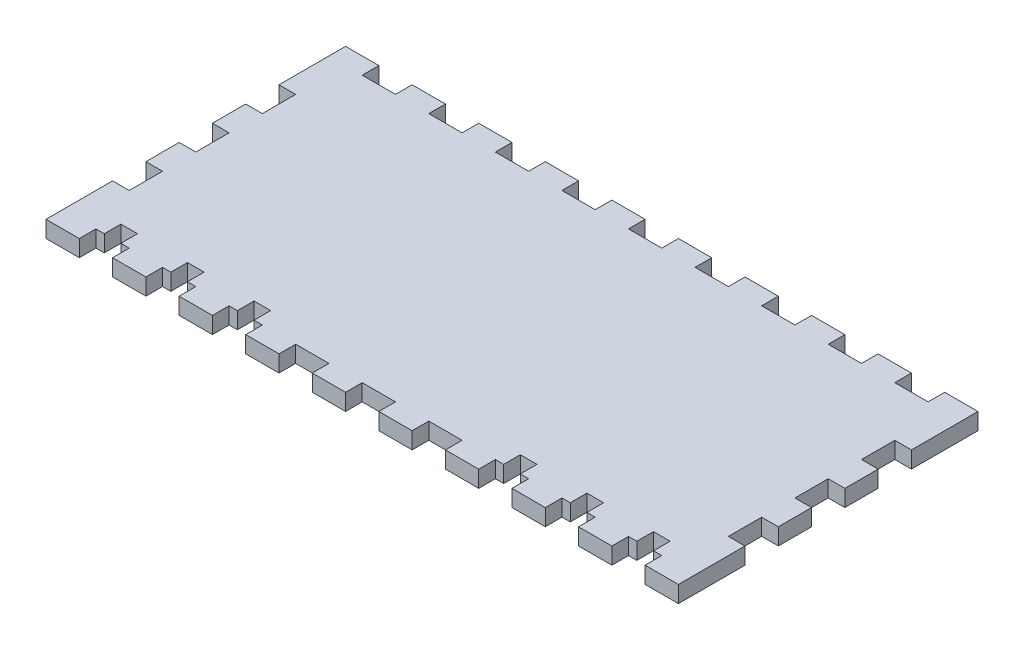
SolidWorks part; units mm, degrees
material "Pine"
ref_plane "Front Plane" through (0, 0, 0) normal (0, 0, 1) x (1, 0, 0)
ref_plane "Top Plane" through (0, 0, 0) normal (0, 1, 0) x (1, 0, 0)
ref_plane "Right Plane" through (0, 0, 0) normal (1, 0, 0) x (0, 0, -1)
sketch "Sketch1" plane through (0, 0, 0) normal (0, 1, 0) x (1, 0, 0)
  line L1 (0, 0) -> (241.3, 0)
  line L2 (0, 0) -> (0, 114.3)
  line L3 (0, 114.3) -> (241.3, 114.3)
  line L4 (241.3, 0) -> (241.3, 114.3)
  dimension "D1" = 114.3
  dimension "D2" = 241.3
extrude "Boss-Extrude1" add sketch "Sketch1" along normal blind 6.35
sketch "Sketch2" plane through (0, 6.35, 0) normal (0, 1, 0) x (1, 0, 0)
  line L0 (25.4, 114.3) -> (12.7, 114.3)
  line L1 (0, 114.3) -> (-12.7, 114.3)
  line L2 (0, 114.3) -> (0, 107.95)
  line L3 (0, 107.95) -> (-12.7, 107.95)
  line L4 (-12.7, 114.3) -> (-12.7, 107.95)
  line L5 (0, 0) -> (-12.7, 0)
  line L6 (0, 0) -> (0, 6.35)
  line L7 (0, 6.35) -> (-12.7, 6.35)
  line L8 (-12.7, 0) -> (-12.7, 6.35)
  line L9 (25.4, 114.3) -> (25.4, 107.95)
  line L10 (25.4, 107.95) -> (12.7, 107.95)
  line L11 (12.7, 114.3) -> (12.7, 107.95)
  line L12 (25.4, 0) -> (12.7, 0)
  line L13 (25.4, 0) -> (25.4, 6.35)
  line L14 (25.4, 6.35) -> (12.7, 6.35)
  line L15 (12.7, 0) -> (12.7, 6.35)
  line L16 (50.8, 114.3) -> (38.1, 114.3)
  line L17 (50.8, 114.3) -> (50.8, 107.95)
  line L18 (50.8, 107.95) -> (38.1, 107.95)
  line L19 (38.1, 114.3) -> (38.1, 107.95)
  line L20 (50.8, 0) -> (38.1, 0)
  line L21 (50.8, 0) -> (50.8, 6.35)
  line L22 (50.8, 6.35) -> (38.1, 6.35)
  line L23 (38.1, 0) -> (38.1, 6.35)
  line L24 (76.2, 114.3) -> (63.5, 114.3)
  line L25 (76.2, 114.3) -> (76.2, 107.95)
  line L26 (76.2, 107.95) -> (63.5, 107.95)
  line L27 (63.5, 114.3) -> (63.5, 107.95)
  line L28 (76.2, 0) -> (63.5, 0)
  line L29 (76.2, 0) -> (76.2, 6.35)
  line L30 (76.2, 6.35) -> (63.5, 6.35)
  line L31 (63.5, 0) -> (63.5, 6.35)
  line L32 (101.6, 114.3) -> (88.9, 114.3)
  line L33 (101.6, 114.3) -> (101.6, 107.95)
  line L34 (101.6, 107.95) -> (88.9, 107.95)
  line L35 (88.9, 114.3) -> (88.9, 107.95)
  line L36 (101.6, 0) -> (88.9, 0)
  line L37 (101.6, 0) -> (101.6, 6.35)
  line L38 (101.6, 6.35) -> (88.9, 6.35)
  line L39 (88.9, 0) -> (88.9, 6.35)
  line L40 (127, 114.3) -> (114.3, 114.3)
  line L41 (127, 114.3) -> (127, 107.95)
  line L42 (127, 107.95) -> (114.3, 107.95)
  line L43 (114.3, 114.3) -> (114.3, 107.95)
  line L44 (127, 0) -> (114.3, 0)
  line L45 (127, 0) -> (127, 6.35)
  line L46 (127, 6.35) -> (114.3, 6.35)
  line L47 (114.3, 0) -> (114.3, 6.35)
  line L48 (152.4, 114.3) -> (139.7, 114.3)
  line L49 (152.4, 114.3) -> (152.4, 107.95)
  line L50 (152.4, 107.95) -> (139.7, 107.95)
  line L51 (139.7, 114.3) -> (139.7, 107.95)
  line L52 (152.4, 0) -> (139.7, 0)
  line L53 (152.4, 0) -> (152.4, 6.35)
  line L54 (152.4, 6.35) -> (139.7, 6.35)
  line L55 (139.7, 0) -> (139.7, 6.35)
  line L56 (177.8, 114.3) -> (165.1, 114.3)
  line L57 (177.8, 114.3) -> (177.8, 107.95)
  line L58 (177.8, 107.95) -> (165.1, 107.95)
  line L59 (165.1, 114.3) -> (165.1, 107.95)
  line L60 (177.8, 0) -> (165.1, 0)
  line L61 (177.8, 0) -> (177.8, 6.35)
  line L62 (177.8, 6.35) -> (165.1, 6.35)
  line L63 (165.1, 0) -> (165.1, 6.35)
  line L64 (203.2, 114.3) -> (190.5, 114.3)
  line L65 (203.2, 114.3) -> (203.2, 107.95)
  line L66 (203.2, 107.95) -> (190.5, 107.95)
  line L67 (190.5, 114.3) -> (190.5, 107.95)
  line L68 (203.2, 0) -> (190.5, 0)
  line L69 (203.2, 0) -> (203.2, 6.35)
  line L70 (203.2, 6.35) -> (190.5, 6.35)
  line L71 (190.5, 0) -> (190.5, 6.35)
  line L72 (228.6, 114.3) -> (215.9, 114.3)
  line L73 (228.6, 114.3) -> (228.6, 107.95)
  line L74 (228.6, 107.95) -> (215.9, 107.95)
  line L75 (215.9, 114.3) -> (215.9, 107.95)
  line L76 (228.6, 0) -> (215.9, 0)
  line L77 (228.6, 0) -> (228.6, 6.35)
  line L78 (228.6, 6.35) -> (215.9, 6.35)
  line L79 (215.9, 0) -> (215.9, 6.35)
  dimension "D1" = 12.7
  dimension "D2" = 6.35
  dimension "D3" = 10
extrude "Cut-Extrude1" cut sketch "Sketch2" against normal through all
sketch "Sketch3" plane through (0, 6.35, 0) normal (0, 1, 0) x (1, 0, 0)
  line L0 (241.3, 0) -> (241.3, 114.3) construction
  line L1 (0, 63.5) -> (6.35, 63.5)
  line L2 (0, 63.5) -> (0, 50.8)
  line L3 (0, 50.8) -> (6.35, 50.8)
  line L4 (6.35, 63.5) -> (6.35, 50.8)
  line L5 (241.3, 63.5) -> (234.95, 63.5)
  line L6 (241.3, 63.5) -> (241.3, 50.8)
  line L7 (241.3, 50.8) -> (234.95, 50.8)
  line L8 (234.95, 63.5) -> (234.95, 50.8)
  line L9 (0, 114.3) -> (0, 0) construction
  line L10 (12.7, 107.95) -> (25.4, 107.95) construction
  line L11 (12.7, 114.3) -> (12.7, 107.95) construction
  point P8 (0, 57.15)
  point P9 (241.3, 57.15)
extrude "Cut-Extrude2" cut sketch "Sketch3" against normal through all
pattern_linear "LPattern1" count 2 spacing 25.4 along (0, 0, 1) count 2 spacing 25.4 along (0, 0, -1) of "Cut-Extrude2"
sketch "Sketch4" plane through (0, 6.35, 0) normal (0, 1, 0) x (1, 0, 0)
  line L1 (15.875, 12.7) -> (22.225, 12.7)
  line L2 (15.875, 12.7) -> (15.875, 6.35)
  line L3 (15.875, 6.35) -> (22.225, 6.35)
  line L4 (22.225, 12.7) -> (22.225, 6.35)
  line L5 (25.4, 107.95) -> (25.4, 114.3) construction
  line L6 (25.4, 6.35) -> (12.7, 6.35) construction
  point P6 (25.4, 111.125)
  dimension "D1" = 6.35
  dimension "D2" = 3.175
extrude "Cut-Extrude3" cut sketch "Sketch4" against normal through all
pattern_linear "LPattern2" count 9 spacing 25.4 along (1, 0, 0) skipping (3, 0), (4, 0), (5, 0) of "Cut-Extrude3"
